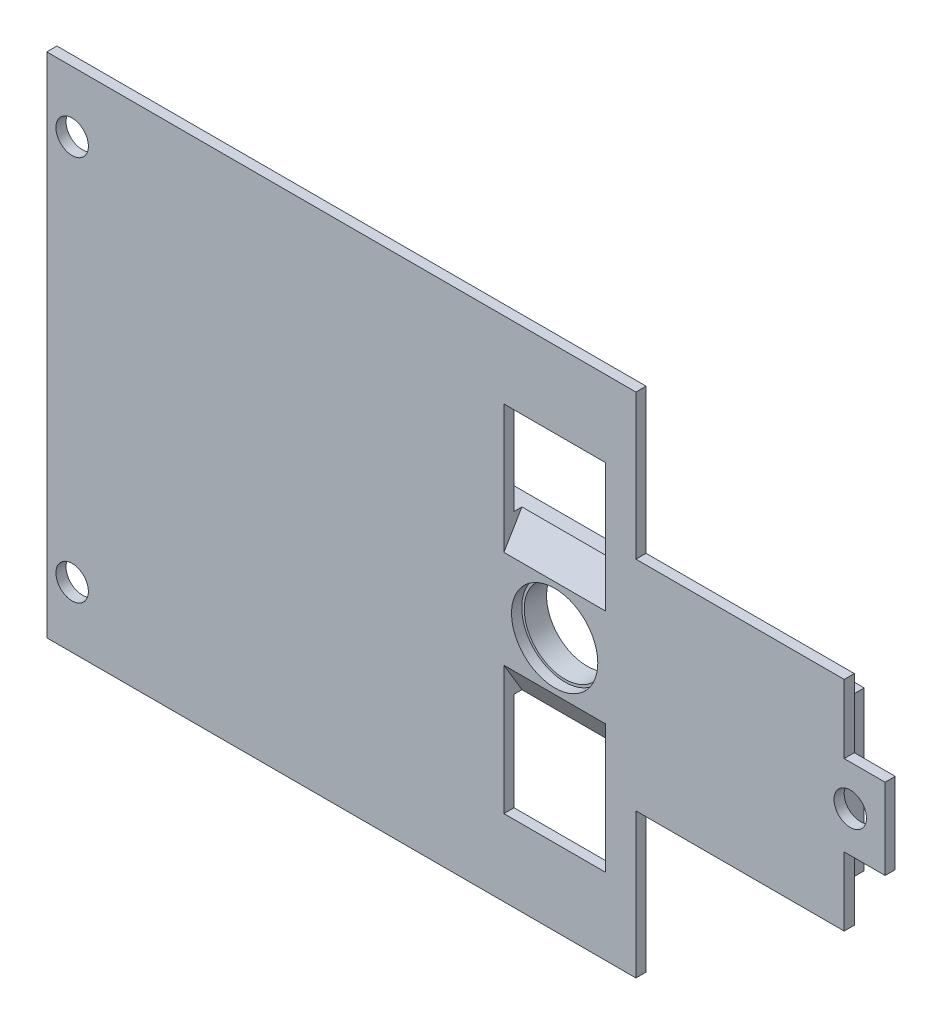
SolidWorks part; units mm, degrees
ref_plane "Front Plane" through (0, 0, 0) normal (0, 0, 1) x (1, 0, 0)
ref_plane "Top Plane" through (0, 0, 0) normal (0, 1, 0) x (1, 0, 0)
ref_plane "Right Plane" through (0, 0, 0) normal (1, 0, 0) x (0, 0, -1)
sketch "Sketch4" plane through (0, 0, 0) normal (0, 0, 1) x (1, 0, 0)
  line L0 (-50.0428, 25) -> (8.0068, 25)
  line L1 (8.0068, 25) -> (8.0068, 10.7378)
  line L2 (8.0068, 10.7378) -> (28.5244, 10.7378)
  line L3 (28.5244, 10.7378) -> (28.5244, 3.982)
  line L4 (0, 0) -> (-58.4806, 0) construction
  line L5 (28.5244, 3.982) -> (32.5554, 3.982)
  line L7 (32.5554, 3.982) -> (32.5554, -3.982)
  line L9 (32.5554, -3.982) -> (28.5244, -3.982)
  line L10 (28.5244, -3.982) -> (28.5244, -10.7378)
  line L11 (28.5244, -10.7378) -> (8.0068, -10.7378)
  line L12 (8.0068, -10.7378) -> (8.0068, -25)
  line L13 (8.0068, -25) -> (-50.0428, -25)
  line L14 (-50.0428, -25) -> (-50.0428, 25)
  line L15 (-5.0043, 17.4777) -> (-5.0043, -17.4777) construction
  line L16 (-5.0043, -17.4777) -> (5.0043, -17.4777) construction
  line L17 (5.0043, -17.4777) -> (5.0043, 17.4777) construction
  line L18 (5.0043, 17.4777) -> (-5.0043, 17.4777) construction
  line L19 (-5.0043, 6.0051) -> (5.0043, 6.0051) construction
  line L21 (-5.0043, -6.0051) -> (5.0043, -6.0051) construction
  line L23 (-10.1394, 8.0068) -> (27.5235, 8.0068) construction
  line L24 (27.5235, 8.0068) -> (27.5235, -8.0068) construction
  line L25 (27.5235, -8.0068) -> (-10.1394, -8.0068) construction
  line L28 (-42.7789, -23.0197) -> (-8.0068, -23.0197) construction
  circle A0 centre (-47.5428, 19) radius 1.6
  circle A1 centre (-47.5428, -19) radius 1.6
  circle A2 centre (29.1235, 0) radius 1.6
  dimension "D1" = 38
  dimension "D3" = 3.2
  dimension "D5" = 3.2
  dimension "D2" = 2.5
  dimension "D4" = 50
extrude "Boss-Extrude2" add sketch "Sketch4" along normal blind 1
sketch "Sketch5" plane through (0, 0, 0) normal (0, 0, -1) x (-1, 0, 0)
  line L5 (10.1307, 7.8) -> (-27.3, 7.8)
  line L7 (-37.7756, 0) -> (61.1931, 0) construction
  line L8 (10.4164, 22.8) -> (42.5753, 22.8)
  line L10 (42.5753, 22.8) -> (42.5753, 12.3)
  line L13 (-8.0068, 25) -> (50.0428, 25) construction
  line L14 (10.4164, 22.8) -> (10.4164, 8)
  line L17 (10.4164, -8) -> (10.4164, -25)
  line L18 (-27.3, 7.8) -> (-27.3, -7.8)
  line L19 (-27.3, -7.8) -> (10.1307, -7.8)
  line L27 (10.1307, 7.8) -> (10.6164, 7.8) construction
  line L28 (10.6164, 22.6) -> (10.6164, 7.8) construction
  line L29 (10.1307, -7.8) -> (10.6164, -7.8) construction
  line L30 (10.6164, -7.8) -> (10.6164, -24.8) construction
  line L31 (10.6164, -24.8) -> (42.3753, -24.8) construction
  line L32 (42.3753, 22.6) -> (42.3753, -24.8) construction
  line L33 (10.6164, 22.6) -> (42.3753, 22.6) construction
  line L34 (10.1307, 7.8) -> (10.4164, 7.8)
  line L35 (10.4164, 7.8) -> (10.4164, 8)
  line L36 (-27.5, 8) -> (-27.5, -8) construction
  line L37 (10.1307, 8) -> (10.4164, 8) construction
  line L38 (10.1307, 8) -> (-27.5, 8) construction
  line L39 (-27.5, -8) -> (10.1307, -8) construction
  line L40 (10.1307, -8) -> (10.4164, -8) construction
  line L41 (10.1307, -7.8) -> (10.4164, -7.8)
  line L42 (10.4164, -7.8) -> (10.4164, -8)
  line L43 (42.5753, 12.3) -> (50.0428, 12.3)
  line L44 (50.0428, -25) -> (50.0428, 25) construction
  line L45 (50.0428, 12.3) -> (50.0428, -12.3)
  line L47 (42.5753, 22.8) -> (42.5753, -25) construction
  line L48 (42.5753, -12.3) -> (50.0428, -12.3)
  line L49 (50.0428, 25) -> (50.0428, -25) construction
  line L52 (10.4164, -25) -> (42.5753, -25) construction
  line L53 (10.4164, -25) -> (27.9164, -25)
  line L54 (50.0428, -25) -> (-8.0068, -25) construction
  line L55 (27.9164, -25) -> (27.9164, -22.8)
  line L56 (27.9164, -22.8) -> (42.5753, -22.8)
  line L57 (42.5753, -22.8) -> (42.5753, -12.3)
  point P21 (41.783, -12.3)
  point P38 (50.0428, 0)
  dimension "D1" = 2.2
  dimension "D2" = 17.5
  dimension "D3" = 24.6
  dimension "D4" = 2.2
  dimension "D5" = 7.4674
  dimension "D7" = 77.3428
extrude "Boss-Extrude3" add sketch "Sketch5" along normal blind 2.2
sketch "Sketch6" plane through (0, 0, 1) normal (0, 0, 1) x (1, 0, 0)
  line L0 (-5.0043, 17.4777) -> (-5.0043, -17.4777) construction
  line L5 (-5.0043, -8.0068) -> (5.0043, -8.0068)
  line L6 (-5.0043, -8.0068) -> (-5.0043, -17.4777)
  line L7 (-5.0043, -17.4777) -> (5.0043, -17.4777)
  line L8 (5.0043, -8.0068) -> (5.0043, -17.4777)
  line L9 (27.5235, -8.0068) -> (-10.1394, -8.0068) construction
  line L10 (5.0043, -17.4777) -> (5.0043, 17.4777) construction
  line L11 (-5.0043, 17.4777) -> (5.0043, 17.4777)
  line L12 (-5.0043, 17.4777) -> (-5.0043, 8.0068)
  line L13 (-5.0043, 8.0068) -> (5.0043, 8.0068)
  line L14 (5.0043, 17.4777) -> (5.0043, 8.0068)
  line L15 (-10.1394, 8.0068) -> (27.5235, 8.0068) construction
  circle A0 centre (0, 0) radius 4
  dimension "D1" = 8
extrude "Cut-Extrude1" cut sketch "Sketch6" against normal through all
sketch "Sketch7" plane through (-5.0043, 0, 0) normal (1, 0, 0) x (0, 0, -1)
  line L0 (0.9044, -8.0068) -> (-1, -4.8142)
  line L1 (0, -8.0068) -> (-1, -8.0068) construction
  line L2 (-1, -10.7378) -> (-1, -3.982) construction
  line L3 (-1, -4.8142) -> (-1, -8.0068)
  line L5 (-1, -8.0068) -> (0, -8.0068)
  line L8 (0, -8.0068) -> (0.9044, -8.0068)
  dimension "D2" = 30.816
extrude "Cut-Extrude2" cut sketch "Sketch7" along normal up to surface (10.0086 mm away) up to face at (5.0043, -12.7423, 0.5)
mirror "Mirror1" about plane through (0, 0, 0) normal (0, 1, 0) of "Cut-Extrude2"
sketch "Sketch8" plane through (0, 0, -2.2) normal (0, 0, -1) x (-1, 0, 0)
  line L0 (42.5753, -12.3) -> (50.0428, -12.3) construction
  line L1 (50.0428, 12.3) -> (47.5428, 12.3)
  line L2 (50.0428, 12.3) -> (50.0428, -12.3)
  line L3 (50.0428, -12.3) -> (47.5428, -12.3)
  line L4 (47.5428, 12.3) -> (47.5428, -12.3)
  line L5 (50.0428, -25) -> (50.0428, 25) construction
  dimension "D1" = 2.5
extrude "Boss-Extrude4" add sketch "Sketch8" along normal blind 10
sketch "Sketch9" plane through (-50.0428, 0, 0) normal (-1, 0, 0) x (0, 0, 1)
  line L0 (-9.2, 9.0613) -> (-12.2, 9.0613)
  line L1 (-12.2, -12.3) -> (-12.2, 12.3) construction
  line L2 (-12.2, 9.0613) -> (-12.2, 5.0871)
  line L3 (-12.2, 5.0871) -> (-9.2, 5.0871)
  arc A0 (-9.2, 5.0871) -> (-9.2, 9.0613) centre (-9.2, 7.0742) ccw
  dimension "D1" = 3
extrude "Cut-Extrude3" cut sketch "Sketch9" against normal up to next
sketch "Sketch10" plane through (0, 0, 1) normal (0, 0, 1) x (1, 0, 0)
  circle A0 centre (0, 0) radius 4.25
  dimension "D1" = 8.5
extrude "Cut-Extrude4" cut sketch "Sketch10" against normal blind 1
